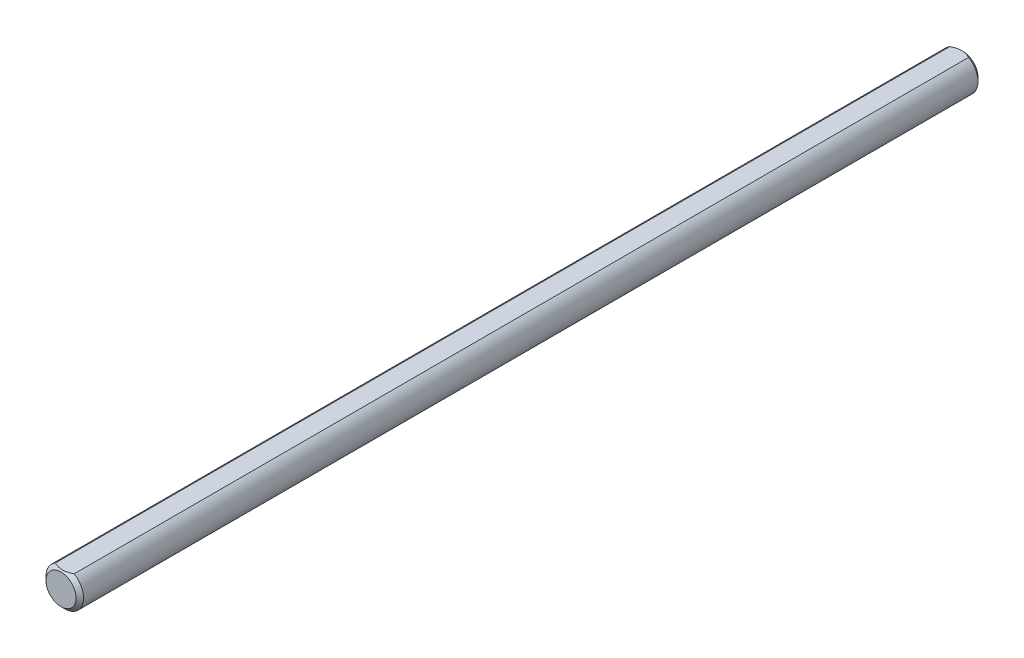
SolidWorks part; units mm, degrees
ref_plane "Front" through (0, 0, 0) normal (0, 0, 1) x (1, 0, 0)
ref_plane "Top" through (0, 0, 0) normal (0, 1, 0) x (1, 0, 0)
ref_plane "Right" through (0, 0, 0) normal (1, 0, 0) x (0, 0, -1)
sketch "Sketch1" plane through (0, 0, 0) normal (0, 0, 1) x (1, 0, 0)
  circle A0 centre (0, 0) radius 3.175
  dimension "D1" = 6.35
extrude "Extrude1" add sketch "Sketch1" along normal mid plane 152.4
chamfer "Chamfer1" distance 0.635 angle 45 2 edges at (3.175, 0, -76.2) (3.175, 0, 76.2)
sketch "Sketch13" plane through (0, 0, 0) normal (0, 0, 1) x (1, 0, 0)
  line L3 (-1.5875, 2.7496) -> (1.5875, 2.7496)
  circle A0 centre (0, 0) radius 3.175 construction
  arc A1 (1.5875, 2.7496) -> (-1.5875, 2.7496) centre (0, 0) ccw
  dimension "D1" = 3.175
extrude "Extrude7" cut sketch "Sketch13" against normal through all and the other way through all
equation "\"D1@Chamfer1\" = \"D1@Sketch1\" * .1"
equation "\"D1@Sketch13\" = \"D1@Sketch1\" * .5"
